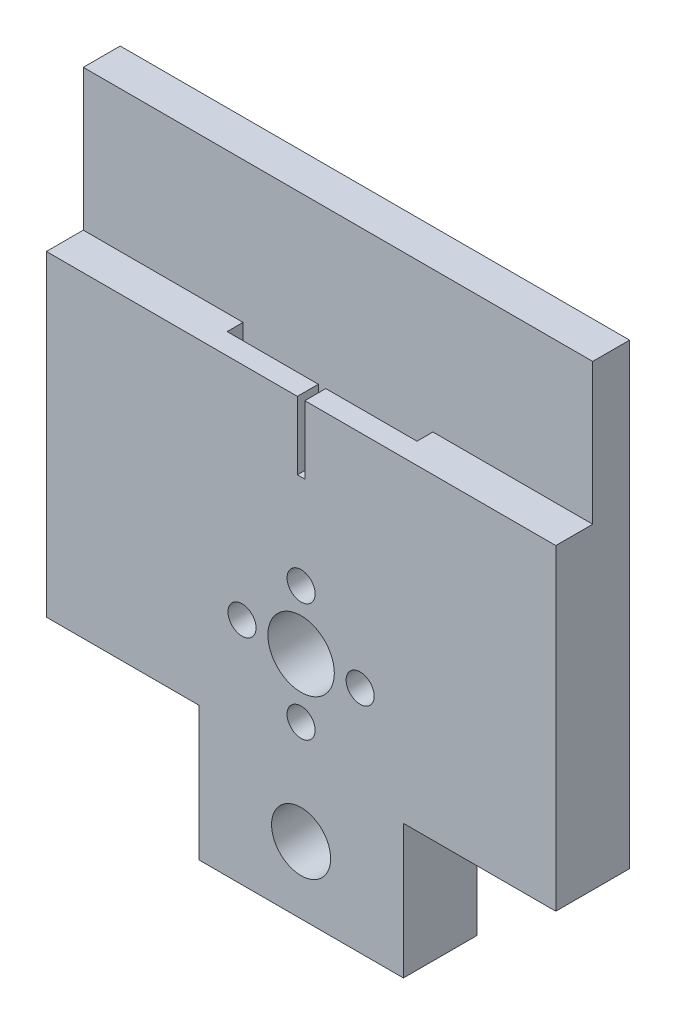
SolidWorks part; units mm, degrees
ref_plane "Front Plane" through (0, 0, 0) normal (0, 0, 1) x (1, 0, 0)
ref_plane "Top Plane" through (0, 0, 0) normal (0, 1, 0) x (1, 0, 0)
ref_plane "Right Plane" through (0, 0, 0) normal (1, 0, 0) x (0, 0, -1)
sketch "Sketch1" plane through (0, 0, 0) normal (0, 0, 1) x (1, 0, 0)
  line L0 (0, 40.0739) -> (0, -40.0739) construction
  line L1 (-34.5, 40.0739) -> (34.5, 40.0739)
  line L2 (34.5, 40.0739) -> (34.5, -21.9261)
  line L3 (34.5, -21.9261) -> (13.8611, -21.9261)
  line L4 (13.8611, -21.9261) -> (13.8611, -40.0739)
  line L5 (13.8611, -40.0739) -> (-13.8611, -40.0739)
  line L6 (-13.8611, -21.9261) -> (-13.8611, -40.0739)
  line L7 (-34.5, -21.9261) -> (-13.8611, -21.9261)
  line L8 (-34.5, 40.0739) -> (-34.5, -21.9261)
  dimension "D1" = 69
  dimension "D2" = 27.7222
  dimension "D3" = 18.1478
  dimension "D4" = 62
extrude "Boss-Extrude1" add sketch "Sketch1" along normal blind 10
sketch "Sketch2" plane through (0, 0, 10) normal (0, 0, 1) x (1, 0, 0)
  line L0 (0, 40.0739) -> (0, -40.0739) construction
  line L1 (34.5, 40.0739) -> (-34.5, 40.0739) construction
  line L2 (-13.8611, -40.0739) -> (13.8611, -40.0739) construction
  line L3 (-13.8611, -31) -> (13.8611, -31) construction
  line L4 (-13.8611, -21.9261) -> (-13.8611, -40.0739) construction
  line L5 (13.8611, -40.0739) -> (13.8611, -21.9261) construction
  line L7 (-34.5, 40.0739) -> (-34.5, -21.9261) construction
  line L8 (34.5, -21.9261) -> (34.5, 40.0739) construction
  line L9 (-34.5, 32.3714) -> (34.5, 32.3714) construction
  circle A0 centre (0, -31) radius 4
  circle A1 centre (0, -9) radius 4.5
  circle A2 centre (0, -1) radius 1.9
  circle A6 centre (8, -9) radius 1.9
  circle A7 centre (0, -17) radius 1.9
  circle A8 centre (-8, -9) radius 1.9
  point P33 (2.405, -11.405)
  point P34 (0, -9)
  dimension "D1" = 9
  dimension "D2" = 8
  dimension "D3" = 22
  dimension "D4" = 3.8
  dimension "D5" = 8
  dimension "D6" = 4
extrude "Cut-Extrude1" cut sketch "Sketch2" against normal through all
sketch "Sketch4" plane through (-34.5, 0, 0) normal (-1, 0, 0) x (0, 0, 1)
  line L0 (5, 40.0739) -> (5, 20.9739)
  line L1 (10, 40.0739) -> (0, 40.0739) construction
  line L2 (5, 20.9739) -> (10, 20.9739)
  line L3 (10, 40.0739) -> (10, -21.9261) construction
  dimension "D1" = 19.1
extrude "Cut-Extrude2" cut sketch "Sketch4" against normal through all and the other way through all
sketch "Sketch5" plane through (0, 0, 10) normal (0, 0, 1) x (1, 0, 0)
  line L0 (0, 20.9739) -> (0, -4.5) construction
  line L1 (-34.5, 20.9739) -> (34.5, 20.9739) construction
  line L2 (-0.508, 20.9739) -> (-0.508, 11.7664)
  line L3 (-34.5, 20.9739) -> (34.5, 20.9739) construction
  line L4 (-0.508, 11.7664) -> (0.508, 11.7664)
  line L5 (-0.508, 20.9739) -> (0.508, 20.9739)
  line L6 (0.508, 20.9739) -> (0.508, 11.7664)
  circle A0 centre (0, -9) radius 4.5 construction
  point P13 (0, 11.7664)
  dimension "D1" = 9.2075
  dimension "D2" = 0.508
extrude "Cut-Extrude4" cut sketch "Sketch5" against normal blind 5
sketch "Sketch6" plane through (0, 20.9739, 0) normal (0, 1, 0) x (1, 0, 0)
  line L0 (-12.858, -5) -> (-12.858, -7.159)
  line L1 (-34.5, -5) -> (-0.508, -5) construction
  line L2 (-12.858, -7.159) -> (-0.508, -7.159)
  line L3 (-0.508, -5) -> (-0.508, -10) construction
  line L4 (-12.858, -5) -> (-0.508, -5)
  line L5 (-0.508, -5) -> (-0.508, -7.159)
  dimension "D1" = 12.35
  dimension "D2" = 2.159
extrude "Cut-Extrude5" cut sketch "Sketch6" against normal blind 9.954
sketch "Sketch7" plane through (0, 20.9739, 0) normal (0, 1, 0) x (1, 0, 0)
  line L0 (12.858, -5) -> (12.858, -7.159)
  line L1 (0.508, -5) -> (34.5, -5) construction
  line L2 (12.858, -7.159) -> (0.508, -7.159)
  line L3 (0.508, -5) -> (0.508, -10) construction
  line L4 (0.508, -7.159) -> (0.508, -5)
  line L5 (0.508, -5) -> (12.858, -5)
  dimension "D1" = 12.35
  dimension "D2" = 2.159
extrude "Cut-Extrude6" cut sketch "Sketch7" against normal blind 9.954
